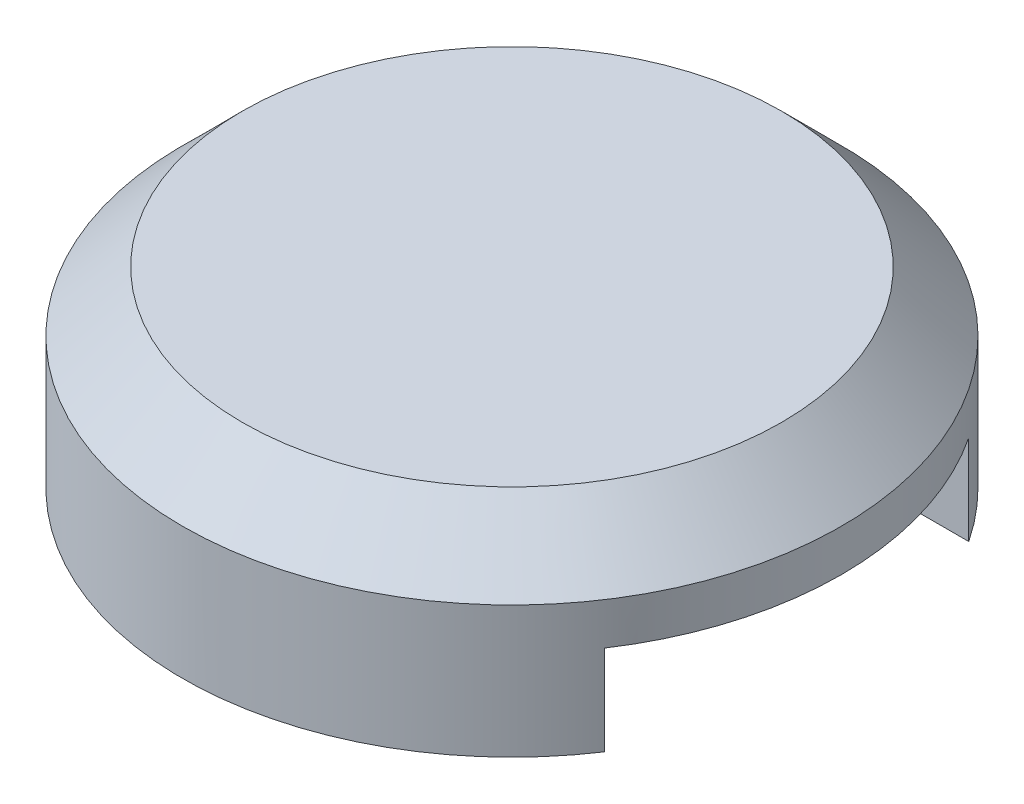
SolidWorks part; units mm, degrees
ref_plane "Front Plane" through (0, 0, 0) normal (0, 0, 1) x (1, 0, 0)
ref_plane "Top Plane" through (0, 0, 0) normal (0, 1, 0) x (1, 0, 0)
ref_plane "Right Plane" through (0, 0, 0) normal (1, 0, 0) x (0, 0, -1)
sketch "Sketch1" plane through (0, 0, 0) normal (0, 1, 0) x (1, 0, 0)
  circle A0 centre (0, 0) radius 5.5
  dimension "D1" = 11
extrude "Boss-Extrude1" add sketch "Sketch1" along normal blind 3.2
chamfer "Chamfer2" distance 1 angle 45 1 edges at (0, 3.2, 5.5)
shell "Shell1" thickness 1.2
sketch "Sketch4" plane through (0, 0, 0) normal (0, -1, 0) x (1, 0, 0)
  line L1 (3.0406, -3.0406) -> (-3.0406, -3.0406) construction
  line L2 (3.0406, -3.0406) -> (3.0406, 3.0406) construction
  line L3 (3.0406, 3.0406) -> (-3.0406, 3.0406) construction
  line L4 (-3.0406, -3.0406) -> (-3.0406, 3.0406) construction
  line L5 (3.0406, -3.0406) -> (-3.0406, 3.0406) construction
  line L6 (3.0406, 3.0406) -> (-3.0406, -3.0406) construction
  line L7 (3.0406, 3.0406) -> (9.1217, 3.0406)
  line L8 (3.0406, 3.0406) -> (3.0406, -3.0406)
  line L9 (3.0406, -3.0406) -> (9.1217, -3.0406)
  line L10 (9.1217, 3.0406) -> (9.1217, -3.0406)
  circle A0 centre (0, 0) radius 4.3 construction
  point P0 (0, 0)
  point P6 (3.0926, -2.9876)
extrude "Cut-Extrude1" cut sketch "Sketch4" against normal blind 1.5
